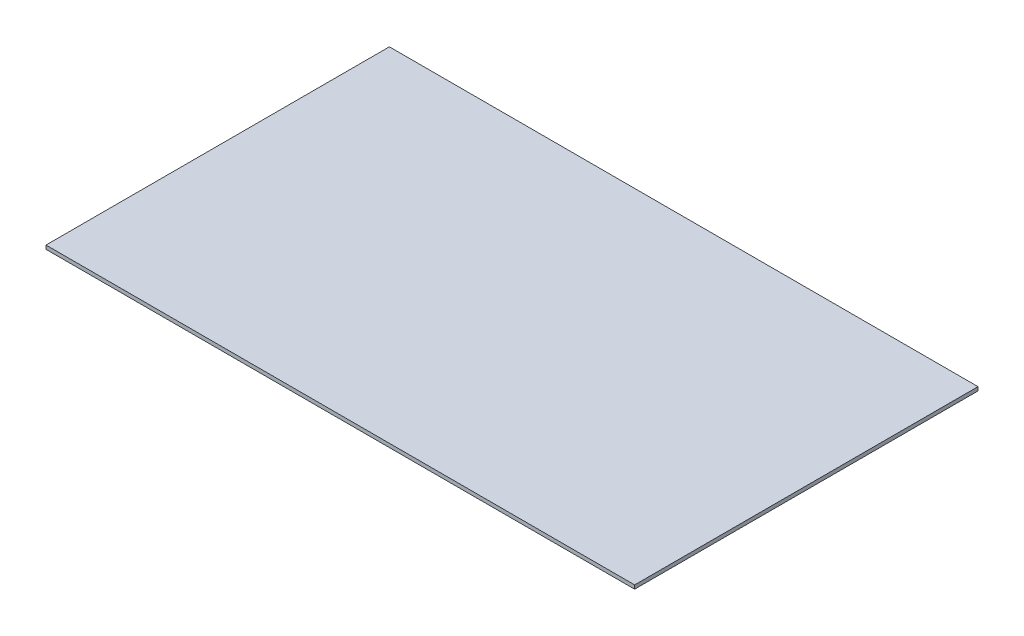
SolidWorks part; units mm, degrees
ref_plane "Front Plane" through (0, 0, 0) normal (0, 0, 1) x (1, 0, 0)
ref_plane "Top Plane" through (0, 0, 0) normal (0, 1, 0) x (1, 0, 0)
ref_plane "Right Plane" through (0, 0, 0) normal (1, 0, 0) x (0, 0, -1)
sketch "Sketch1" plane through (0, 0, 0) normal (0, 1, 0) x (1, 0, 0)
  line L1 (0, 0) -> (60, 0)
  line L2 (0, 0) -> (0, 35)
  line L3 (0, 35) -> (60, 35)
  line L4 (60, 0) -> (60, 35)
  circle A0 centre (30, 17.5) radius 1 construction
  point P8 (30, 35)
  point P10 (0, 17.5)
  dimension "D3" = 2
  dimension "D1" = 35
  dimension "D2" = 60
extrude "Boss-Extrude1" add sketch "Sketch1" along normal blind 0.381
